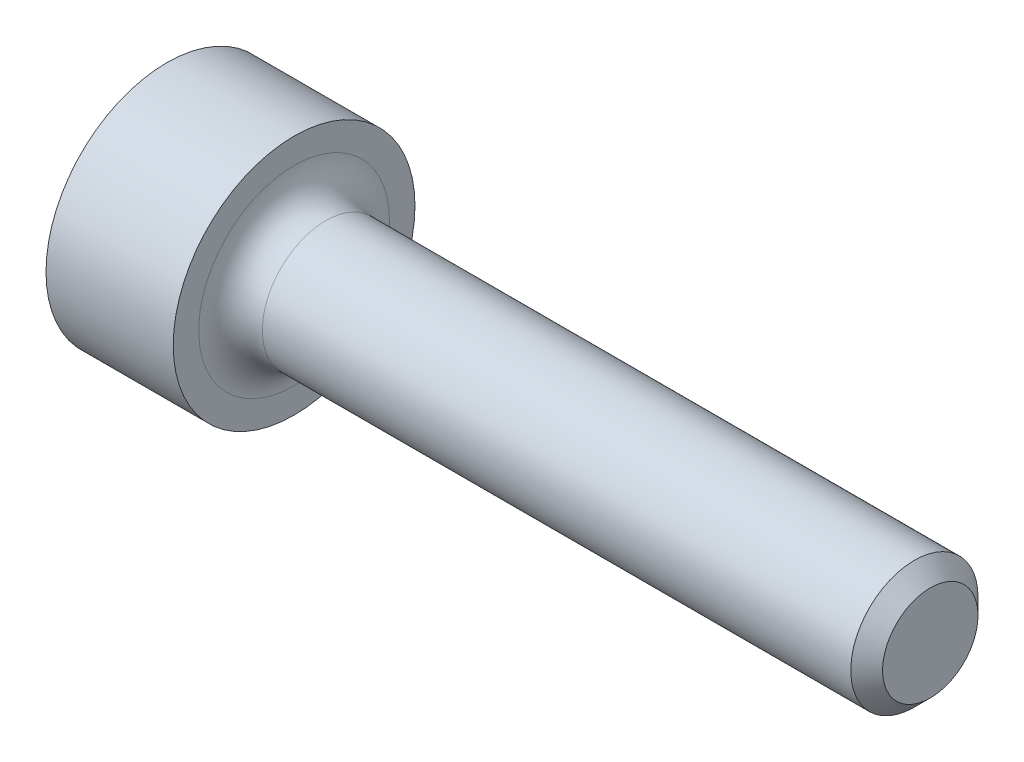
SolidWorks part; units mm, degrees
material "Простая углеродистая сталь"
ref_plane "Спереди" through (0, 0, 0) normal (0, 0, 1) x (1, 0, 0)
ref_plane "Сверху" through (0, 0, 0) normal (0, 1, 0) x (1, 0, 0)
ref_plane "Справа" through (0, 0, 0) normal (1, 0, 0) x (0, 0, -1)
sketch "Эскиз2" plane through (0, 0, 0) normal (0, 0, 1) x (1, 0, 0)
  line L0 (0, 0) -> (0, -1.9)
  line L1 (0, -1.9) -> (2, -1.9)
  line L2 (2, -1.9) -> (2, -1)
  line L3 (2, -1) -> (12, -1)
  line L4 (12, 0) -> (12, -1)
  line L5 (0, 0) -> (12, 0)
  dimension "D3" = 10
  dimension "D1" = 1.9
  dimension "D2" = 2
  dimension "D4" = 0.9
revolve "Повернуть1" add sketch "Эскиз2" angle 360 about L5
fillet "Скругление1" radius 0.5 1 edges at (2, 0, 1)
sketch "Эскиз3" plane through (0, 0, 0) normal (-1, 0, 0) x (0, 0, 1)
  line L1 (0, 0.866) -> (-0.75, 0.433)
  line L2 (-0.75, 0.433) -> (-0.75, -0.433)
  line L3 (-0.75, -0.433) -> (0, -0.866)
  line L4 (0, -0.866) -> (0.75, -0.433)
  line L5 (0.75, -0.433) -> (0.75, 0.433)
  line L6 (0.75, 0.433) -> (0, 0.866)
  circle A1 centre (0, 0) radius 0.75 construction
  dimension "D1" = 1.5
  dimension "D2" = 1.5
  dimension "D3" = 120
extrude "Вырез-Вытянуть2" cut sketch "Эскиз3" against normal blind 1
sketch "Эскиз5" plane through (0, 0, 0) normal (0, 0, 1) x (1, 0, 0)
  line L0 (0, -0.433) -> (0, -0.866) construction
  line L2 (1, -0.866) -> (1, 0)
  line L3 (1, 0) -> (1.5, 0)
  line L4 (1.5, 0) -> (1, -0.866)
  dimension "D1" = 60
  dimension "D2" = 1
revolve "Вырез-Повернуть1" cut sketch "Эскиз5" angle 360 about L3
chamfer "Фаска3" distance 0.25 angle 45 1 edges at (12, 0, 1)
